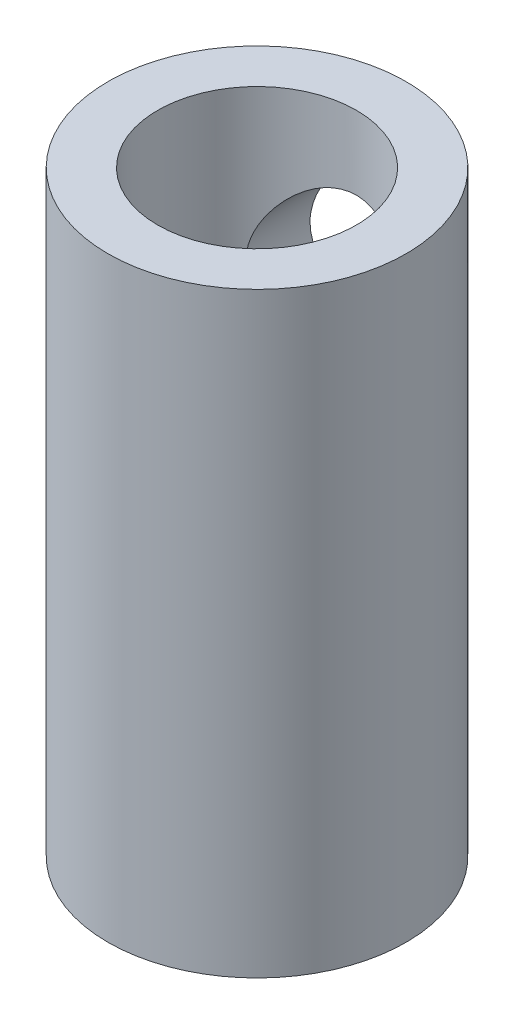
SolidWorks part; units mm, degrees
ref_plane "Front Plane" through (0, 0, 0) normal (0, 0, 1) x (1, 0, 0)
ref_plane "Top Plane" through (0, 0, 0) normal (0, 1, 0) x (1, 0, 0)
ref_plane "Right Plane" through (0, 0, 0) normal (1, 0, 0) x (0, 0, -1)
sketch "Sketch1" plane through (0, 0, 0) normal (0, 1, 0) x (1, 0, 0)
  circle A0 centre (0, 0) radius 4.7625
  dimension "D1" = 9.525
extrude "Boss-Extrude1" add sketch "Sketch1" along normal blind 19.05
sketch "Sketch2" plane through (0, 0, 0) normal (0, -1, 0) x (1, 0, 0)
  circle A0 centre (0, 0) radius 3
  dimension "D1" = 6
extrude "Cut-Extrude1" cut sketch "Sketch2" against normal blind 9.525
sketch "Sketch3" plane through (0, 19.05, 0) normal (0, 1, 0) x (1, 0, 0)
  circle A0 centre (0, 0) radius 3.175
  dimension "D1" = 6.35
extrude "Cut-Extrude2" cut sketch "Sketch3" against normal blind 9.525
ref_plane "Plane1" through (0, 0, -4.7625) normal (0, 0, -1) x (-1, 0, 0)
sketch "Sketch4" plane through (0, 0, -4.7625) normal (0, 0, -1) x (-1, 0, 0)
  line L0 (4.7625, 19.05) -> (-4.7625, 19.05) construction
  line L1 (-4.7625, 0) -> (4.7625, 0) construction
  circle A0 centre (0, 14.2875) radius 2.413
  circle A1 centre (0, 4.7625) radius 2.413
  dimension "D1" = 4.826
  dimension "D2" = 4.7625
  dimension "D3" = 4.7625
extrude "Cut-Extrude3" cut sketch "Sketch4" against normal up to surface (2.98 mm away)
